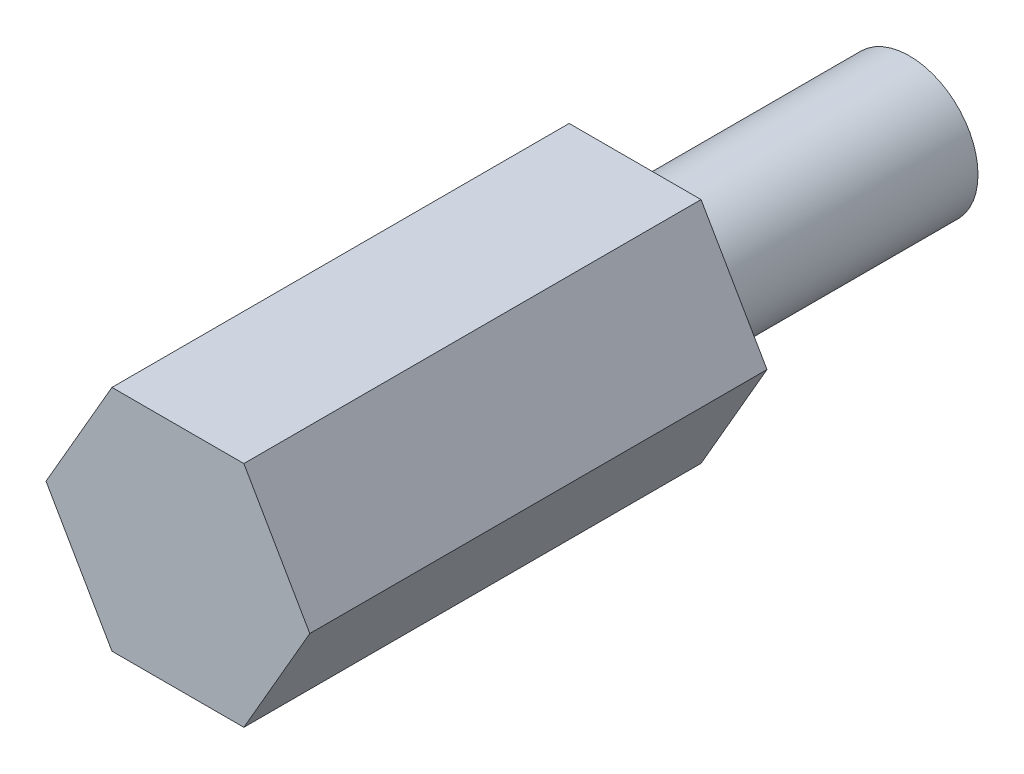
SolidWorks part; units mm, degrees
ref_plane "Alzado" through (0, 0, 0) normal (0, 0, 1) x (1, 0, 0)
ref_plane "Planta" through (0, 0, 0) normal (0, 1, 0) x (1, 0, 0)
ref_plane "Vista lateral" through (0, 0, 0) normal (1, 0, 0) x (0, 0, -1)
sketch "0" plane through (0, 0, 0) normal (0, 0, 1) x (1, 0, 0)
  line L0 (35.3508, 22.4151) -> (32.4658, 22.4151)
  line L1 (32.4658, 22.4151) -> (31.0233, 19.9167)
  line L2 (31.0233, 19.9167) -> (32.4658, 17.4182)
  line L3 (32.4658, 17.4182) -> (35.3508, 17.4182)
  line L4 (35.3508, 17.4182) -> (36.7933, 19.9167)
  line L5 (36.7933, 19.9167) -> (35.3508, 22.4151)
sketch "Corte exterior" plane through (0, 0, 0) normal (0, 0, 1) x (1, 0, 0)
  circle A0 centre (33.9083, 19.9167) radius 1.5
extrude "Saliente-Extruir1" add sketch "0" along normal blind 10
extrude "Saliente-Extruir2" add sketch "Corte exterior" against normal blind 6
